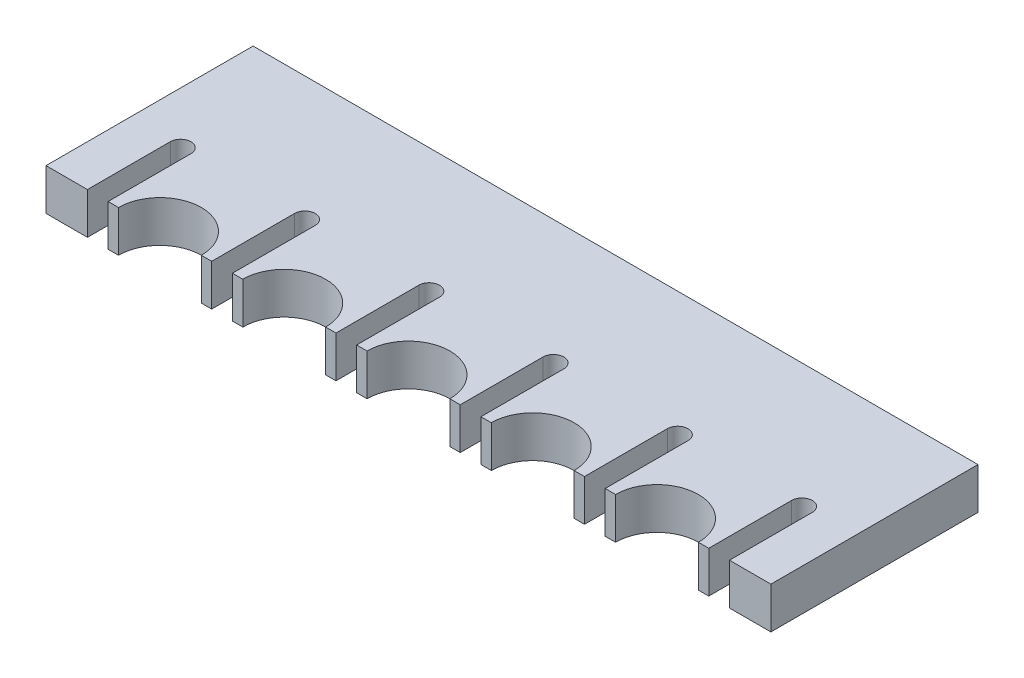
SolidWorks part; units mm, degrees
ref_plane "Front Plane" through (0, 0, 0) normal (0, 0, 1) x (1, 0, 0)
ref_plane "Top Plane" through (0, 0, 0) normal (0, 1, 0) x (1, 0, 0)
ref_plane "Right Plane" through (0, 0, 0) normal (1, 0, 0) x (0, 0, -1)
sketch "Sketch2" plane through (0, 0, 0) normal (0, 1, 0) x (1, 0, 0)
  line L0 (-77.5, -25) -> (-77.5, -5)
  line L1 (-87.5, 25) -> (87.5, 25)
  line L2 (-87.5, 25) -> (-87.5, -25)
  line L3 (-87.5, -25) -> (-77.5, -25)
  line L4 (87.5, 25) -> (87.5, -25)
  line L5 (-87.5, 25) -> (87.5, -25) construction
  line L6 (-87.5, -25) -> (87.5, 25) construction
  line L7 (-77.5, -5) -> (-72.5, -5) construction
  line L8 (-72.5, -5) -> (-72.5, -25)
  line L9 (-47.5, -25) -> (-47.5, -5)
  line L10 (-42.5, -5) -> (-42.5, -25)
  line L11 (-17.5, -25) -> (-17.5, -5)
  line L12 (-12.5, -5) -> (-12.5, -25)
  line L13 (12.5, -25) -> (12.5, -5)
  line L14 (17.5, -5) -> (17.5, -25)
  line L15 (42.5, -25) -> (42.5, -5)
  line L16 (47.5, -5) -> (47.5, -25)
  line L17 (72.5, -25) -> (72.5, -5)
  line L18 (77.5, -5) -> (77.5, -25)
  line L19 (-72.5, -25) -> (-70, -25)
  line L20 (-42.5, -25) -> (-40, -25)
  line L21 (-12.5, -25) -> (-10, -25)
  line L22 (17.5, -25) -> (20, -25)
  line L23 (47.5, -25) -> (50, -25)
  line L24 (77.5, -25) -> (87.5, -25)
  line L25 (-50, -25) -> (-47.5, -25)
  line L26 (-20, -25) -> (-17.5, -25)
  line L27 (10, -25) -> (12.5, -25)
  line L28 (40, -25) -> (42.5, -25)
  line L29 (70, -25) -> (72.5, -25)
  arc A0 (-72.5, -5) -> (-77.5, -5) centre (-75, -5) ccw
  arc A1 (-42.5, -5) -> (-47.5, -5) centre (-45, -5) ccw
  arc A2 (-12.5, -5) -> (-17.5, -5) centre (-15, -5) ccw
  arc A3 (17.5, -5) -> (12.5, -5) centre (15, -5) ccw
  arc A4 (47.5, -5) -> (42.5, -5) centre (45, -5) ccw
  arc A5 (77.5, -5) -> (72.5, -5) centre (75, -5) ccw
  arc A6 (-50, -25) -> (-70, -25) centre (-60, -25) ccw
  arc A7 (-20, -25) -> (-40, -25) centre (-30, -25) ccw
  arc A8 (10, -25) -> (-10, -25) centre (0, -25) ccw
  arc A9 (40, -25) -> (20, -25) centre (30, -25) ccw
  arc A10 (70, -25) -> (50, -25) centre (60, -25) ccw
  point P0 (0, 0)
  point P39 (-49.636, -25)
  point P40 (-19.7232, -25)
  dimension "D8" = 10
  dimension "D1" = 10
  dimension "D2" = 50
  dimension "D3" = 5
  dimension "D4" = 20
  dimension "D5" = 10
  dimension "D7" = 30
  dimension "D6" = 6
  dimension "D9" = 5
extrude "Boss-Extrude1" add sketch "Sketch2" along normal blind 10
